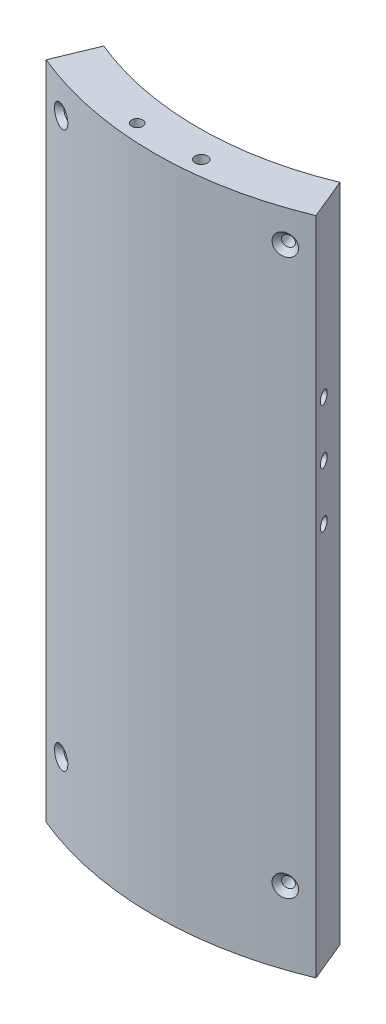
SolidWorks part; units mm, degrees
ref_plane "Front Plane" through (0, 0, 0) normal (0, 0, 1) x (1, 0, 0)
ref_plane "Top Plane" through (0, 0, 0) normal (0, 1, 0) x (1, 0, 0)
ref_plane "Right Plane" through (0, 0, 0) normal (1, 0, 0) x (0, 0, -1)
sketch "Sketch1" plane through (0, 0, 0) normal (0, 1, 0) x (1, 0, 0)
  line L1 (-23.1, -13.65) -> (23.1, -13.65)
  line L2 (-23.1, -13.65) -> (-23.1, 13.65)
  line L3 (-23.1, 13.65) -> (23.1, 13.65)
  line L4 (23.1, -13.65) -> (23.1, 13.65)
  line L5 (-23.1, -13.65) -> (23.1, 13.65) construction
  line L6 (-23.1, 13.65) -> (23.1, -13.65) construction
  point P0 (0, 0)
extrude "Boss-Extrude1" add sketch "Sketch1" along normal blind 107
sketch "Sketch2" plane through (0, 0, 0) normal (0, -1, 0) x (1, 0, 0)
  line L0 (-5.5, 3.65) -> (4.8, 3.65)
  line L5 (-13.1, 1.25) -> (-13.1, -2.25)
  line L6 (-4.4, -3.65) -> (13.1, -3.65)
  line L7 (-4.4, -3.65) -> (-4.4, -2.25)
  line L8 (-4.4, -2.25) -> (-13.1, -2.25)
  line L9 (13.1, -2.15) -> (13.1, -3.65)
  line L10 (-13.1, 1.25) -> (-5.5, 1.25)
  line L11 (-5.5, 1.25) -> (-5.5, 3.65)
  line L13 (4.8, 3.65) -> (4.8, 3.05)
  line L14 (4.8, 3.05) -> (10.4, 3.05)
  line L15 (10.4, 3.05) -> (10.4, 0.45)
  line L16 (10.4, 0.45) -> (11.7, 0.45)
  line L17 (11.7, 0.45) -> (11.7, -2.15)
  line L18 (11.7, -2.15) -> (13.1, -2.15)
  point P0 (0, 0)
extrude "Cut-Extrude1" cut sketch "Sketch2" against normal blind 24
sketch "Sketch3" plane through (0, 24, 0) normal (0, -1, 0) x (1, 0, 0)
  line L0 (-13.1, 1.25) -> (-13.1, -2.25)
  line L1 (-13.1, -2.25) -> (-4.4, -2.25)
  line L2 (-4.4, -2.25) -> (-4.4, -3.65)
  line L3 (-4.4, -3.65) -> (13.1, -3.65)
  line L4 (13.1, -3.65) -> (13.1, -2.15)
  line L5 (13.1, -2.15) -> (11.7, -2.15)
  line L6 (11.7, 0.45) -> (10.4, 0.45)
  line L7 (11.7, 0.45) -> (11.7, -2.15)
  line L8 (10.4, 0.45) -> (10.4, 2.15)
  line L10 (10.4, 0.45) -> (10.4, 3.05) construction
  line L11 (10.4, 2.15) -> (4.8, 2.15)
  line L12 (4.8, 2.15) -> (4.8, 3.65)
  line L13 (4.8, 3.65) -> (-5.5, 3.65)
  line L14 (-5.5, 3.65) -> (-5.5, 1.25)
  line L15 (-13.1, 1.25) -> (-5.5, 1.25)
extrude "Cut-Extrude2" cut sketch "Sketch3" against normal blind 19.2
sketch "Sketch4" plane through (0, 43.2, 0) normal (0, -1, 0) x (1, 0, 0)
  line L0 (-13.1, -2.25) -> (11.7, -2.25)
  line L1 (-13.1, -2.25) -> (-13.1, -0.55)
  line L2 (-13.1, 1.25) -> (-13.1, -2.25) construction
  line L3 (-13.1, -0.55) -> (-9.3, -0.55)
  line L4 (-9.3, -0.55) -> (-9.3, 1.25)
  line L5 (-9.3, 1.25) -> (-5.5, 1.25)
  line L6 (-5.5, 1.25) -> (-5.5, 3.65)
  line L7 (-5.5, 3.65) -> (4.8, 3.65)
  line L8 (4.8, 3.65) -> (4.8, 1.15)
  line L9 (4.8, 1.15) -> (8.9, 1.15)
  line L10 (8.9, 1.15) -> (8.9, -0.55)
  line L11 (8.9, -0.55) -> (11.7, -0.55)
  line L12 (11.7, -2.15) -> (11.7, 0.45) construction
  line L13 (11.7, -0.55) -> (11.7, -2.25)
extrude "Cut-Extrude3" cut sketch "Sketch4" against normal blind 50
sketch "Sketch5" plane through (0, 93.2, 0) normal (0, -1, 0) x (1, 0, 0)
  line L0 (-13.1, -2.25) -> (11.7, -2.25)
  line L1 (11.7, -2.25) -> (11.7, -0.55)
  line L2 (-5.5, 3.65) -> (4.8, 3.65)
  line L3 (4.8, 3.65) -> (4.8, -0.55)
  line L4 (4.8, -0.55) -> (11.7, -0.55)
  line L5 (-5.5, 3.65) -> (-5.5, -0.55)
  line L6 (-5.5, -0.55) -> (-13.1, -0.55)
  line L7 (-13.1, -0.55) -> (-13.1, -2.25)
extrude "Cut-Extrude4" cut sketch "Sketch5" against normal blind 1
sketch "Sketch6" plane through (0, 94.2, 0) normal (0, -1, 0) x (1, 0, 0)
  line L1 (-13.1, -0.55) -> (11.7, -0.55)
  line L2 (-13.1, -0.55) -> (-13.1, -2.25)
  line L3 (-13.1, -2.25) -> (11.7, -2.25)
  line L4 (11.7, -0.55) -> (11.7, -2.25)
extrude "Cut-Extrude5" cut sketch "Sketch6" against normal blind 5.48
fillet "Fillet1" radius 3.1 2 edges at (11.7, 99.68, -1.4) (-13.1, 99.68, -1.4)
sketch "Sketch7" plane through (-23.1, 0, 0) normal (-1, 0, 0) x (0, 0, 1)
  line L1 (13.65, 107) -> (-13.65, 107)
  line L2 (13.65, 107) -> (13.65, 0)
  line L3 (13.65, 0) -> (-13.65, 0)
  line L4 (-13.65, 107) -> (-13.65, 0)
extrude "Boss-Extrude2" add sketch "Sketch7" along normal blind 35.75
sketch "Sketch8" plane through (23.1, 0, 0) normal (1, 0, 0) x (0, 0, -1)
  line L1 (-13.65, 107) -> (13.65, 107)
  line L2 (-13.65, 107) -> (-13.65, 0)
  line L3 (-13.65, 0) -> (13.65, 0)
  line L4 (13.65, 107) -> (13.65, 0)
extrude "Boss-Extrude3" add sketch "Sketch8" along normal blind 35.75
sketch "Sketch9" plane through (0, 0, -13.65) normal (0, 0, -1) x (-1, 0, 0)
  line L1 (-58.85, 0) -> (58.85, 0)
  line L2 (-58.85, 0) -> (-58.85, 107)
  line L3 (-58.85, 107) -> (58.85, 107)
  line L4 (58.85, 0) -> (58.85, 107)
extrude "Boss-Extrude4" add sketch "Sketch9" along normal blind 39.2125
sketch "Sketch10" plane through (0, 0, 0) normal (0, -1, 0) x (1, 0, 0)
  line L2 (-19.0342, -6.8685) -> (-21.7704, -0.2628)
  line L3 (19.2342, -6.8685) -> (21.9704, -0.2628)
  arc A1 (21.9704, -0.2628) -> (-21.7704, -0.2628) centre (0.1, -53.0625) ccw
  arc A2 (19.2342, -6.8685) -> (-19.0342, -6.8685) centre (0.1, -53.0625) ccw
  dimension "D1" = 45
extrude "Cut-Extrude6" cut sketch "Sketch10" against normal up to vertex (107 mm away) flip side to cut
sketch "Sketch14" plane through (-18.6751, 0, -7.7355) normal (-0.9239, 0, -0.3827) x (-0.3827, 0, 0.9239)
  line L0 (5.7509, 80) -> (0.9384, 80)
  line L2 (-49.0616, 107) -> (-49.0616, 73.6066)
  line L3 (0.9384, 107) -> (0.9384, 0) construction
  circle A0 centre (5.7509, 80) radius 1
  circle A1 centre (5.7509, 71.1) radius 1
  circle A2 centre (5.7509, 62.2) radius 1
  dimension "D1" = 3
  dimension "D2" = 2
revolve "Cut-Revolve1" cut sketch "Sketch14" angle 360 about L2
sketch "Sketch15" plane through (0, 107, 0) normal (0, 1, 0) x (1, 0, 0)
  circle A0 centre (4.8, -1.15) radius 1
  circle A1 centre (-5.5, -1.25) radius 0.9
extrude "Cut-Extrude7" cut sketch "Sketch15" against normal blind 50
ref_plane "Plane3" through (-1.6009, 0, 5.7728) normal (-0.2672, 0, 0.9636) x (0, -1, 0)
sketch "Sketch16" plane through (-1.6009, 0, 5.7728) normal (-0.2672, 0, 0.9636) x (0, -1, 0)
  line L0 (-107, -16.9546) -> (-101.7, -16.9546)
  line L1 (-107, 21.1011) -> (-107, -21.0488) construction
hole_wizard "#2-64 Tapped Hole1" positions "3DSketch5" profile "Sketch18" tap size "#2-64" standard "ANSI Inch" end condition up to next
sketch3d "3DSketch5"
  line L0 (-21.7704, 107, -0.2628) -> (-17.4976, 107, -0.2628)
  line L1 (-21.7704, 107, -0.2628) -> (-21.7704, 0, -0.2628) construction
  point P0 (-17.9286, 101.7934, 1.1693)
  dimension "D1" = 4.1
  dimension "D2" = 5.4
sketch "Sketch18" plane through (-17.9286, 101.7934, 1.1693) normal (0, 1, 0) x (0.9489, 0, 0.3155)
  line L0 (0, 0) -> (0, 19.4796)
  line L1 (0, 19.4796) -> (0.889, 19.4796)
  line L2 (0.889, 19.4796) -> (0.889, 0.8382)
  line L3 (0.889, 0.8382) -> (1.7272, 0)
  line L5 (1.7272, 0) -> (0, 0)
  line L6 (-0.889, 0.8382) -> (-1.7272, 0) construction
  line L11 (0, -6.35) -> (0, 107.95) construction
  dimension "Thru Tap Drill Dia." = 1.778
  dimension "Thru Tap Drill Depth" = 19.4796
  dimension "Near C'Sink Dia." = 3.4544
  dimension "Near C'Sink Angle" = 90
cosmetic thread "Hole Thread1" parameters "D2"=2.1844
sketch "Sketch19" plane through (-18.6751, 0, -7.7355) normal (-0.9239, 0, -0.3827) x (-0.3827, 0, 0.9239)
  line L1 (-49.0616, 0) -> (-49.0616, 49.8545)
pattern_circular "CirPattern1" count 2 over 37 about axis through (0.1, 0, -53.0625) along (0, 1, 0) of "#2-64 Tapped Hole1"
cosmetic thread "Hole Thread2" parameters "D2"=2.1844
pattern_linear "LPattern1" count 2 spacing 90 along (0, -1, 0) of "#2-64 Tapped Hole1", "CirPattern1"
cosmetic thread "Hole Thread3" parameters "D2"=2.1844
cosmetic thread "Hole Thread4" parameters "D2"=2.1844
sketch "Sketch25" plane through (0, 0, -2.25) normal (0, 0, 1) x (1, 0, 0)
  circle A0 centre (-9.9075, 95.74) radius 1.15
  circle A1 centre (8.5075, 95.74) radius 1.15
  circle A2 centre (-9.9075, 6.84) radius 1.15
  dimension "D1" = 2
extrude "Cut-Extrude8" cut sketch "Sketch25" along normal blind 4.6 and the other way up to next
sketch "Sketch26" plane through (0, 0, -2.25) normal (0, 0, 1) x (1, 0, 0)
  circle A0 centre (-9.9075, 95.74) radius 1.75
  circle A1 centre (8.5075, 95.74) radius 1.75
  circle A3 centre (-9.9075, 6.84) radius 1.75
ref_plane "Plane5" through (0, 0, -3.25) normal (0, 0, 1) x (1, 0, 0)
extrude "Cut-Extrude10" cut sketch "Sketch26" against normal blind 2 from surface at -1 starting at plane "Plane5"
